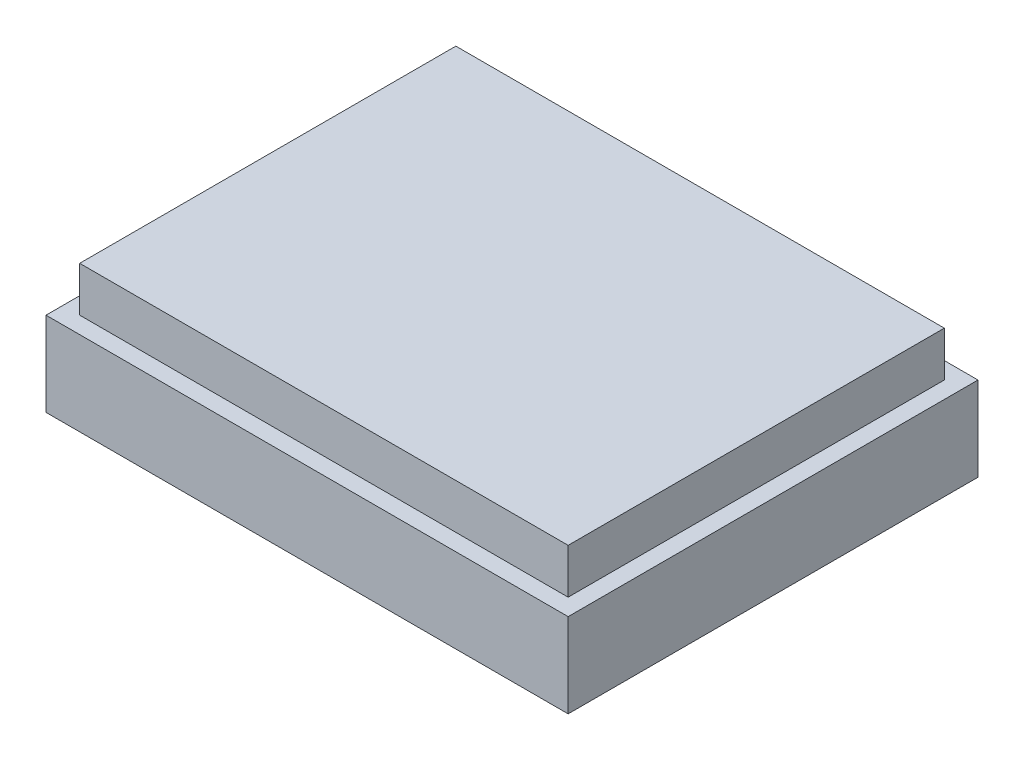
SolidWorks part; units mm, degrees
ref_plane "Front Plane" through (0, 0, 0) normal (0, 0, 1) x (1, 0, 0)
ref_plane "Top Plane" through (0, 0, 0) normal (0, 1, 0) x (1, 0, 0)
ref_plane "Right Plane" through (0, 0, 0) normal (1, 0, 0) x (0, 0, -1)
sketch "Sketch1" plane through (0, 0, 0) normal (0, 1, 0) x (1, 0, 0)
  line L1 (-59.055, 46.355) -> (59.055, 46.355)
  line L2 (-59.055, 46.355) -> (-59.055, -46.355)
  line L3 (-59.055, -46.355) -> (59.055, -46.355)
  line L4 (59.055, 46.355) -> (59.055, -46.355)
  line L5 (-59.055, 46.355) -> (59.055, -46.355) construction
  line L6 (-59.055, -46.355) -> (59.055, 46.355) construction
  point P0 (0, 0)
  dimension "D1" = 118.11
  dimension "D2" = 92.71
extrude "Boss-Extrude1" add sketch "Sketch1" along normal blind 19.05
sketch "Sketch3" plane through (0, 19.05, 0) normal (0, 1, 0) x (1, 0, 0)
  line L8 (55.245, -42.545) -> (55.245, 42.545)
  line L9 (55.245, 42.545) -> (-55.245, 42.545)
  line L10 (-55.245, 42.545) -> (-55.245, -42.545)
  line L11 (-55.245, -42.545) -> (55.245, -42.545)
  line L12 (55.245, -42.545) -> (55.245, 42.545)
  line L13 (55.245, 42.545) -> (-55.245, 42.545)
  line L14 (-55.245, 42.545) -> (-55.245, -42.545)
  line L15 (-55.245, -42.545) -> (55.245, -42.545)
  dimension "D1" = 3.81
extrude "Boss-Extrude2" add sketch "Sketch3" along normal blind 10.16
sketch "Sketch4" plane through (0, 0, -46.355) normal (0, 0, -1) x (-1, 0, 0)
  line L0 (38.1, 9.525) -> (-38.1, 9.525) construction
  line L3 (0, 0) -> (0, 19.05) construction
  line L4 (-59.055, 0) -> (59.055, 0) construction
  line L5 (-59.055, 19.05) -> (59.055, 19.05) construction
  text T0 "TOY TYPE CONVERTERS" font "Century Gothic" height in points 18
  point P7 (0, 9.525)
  dimension "D1" = 76.2
extrude "Cut-Extrude1" cut sketch "Sketch4" against normal blind 2.54
